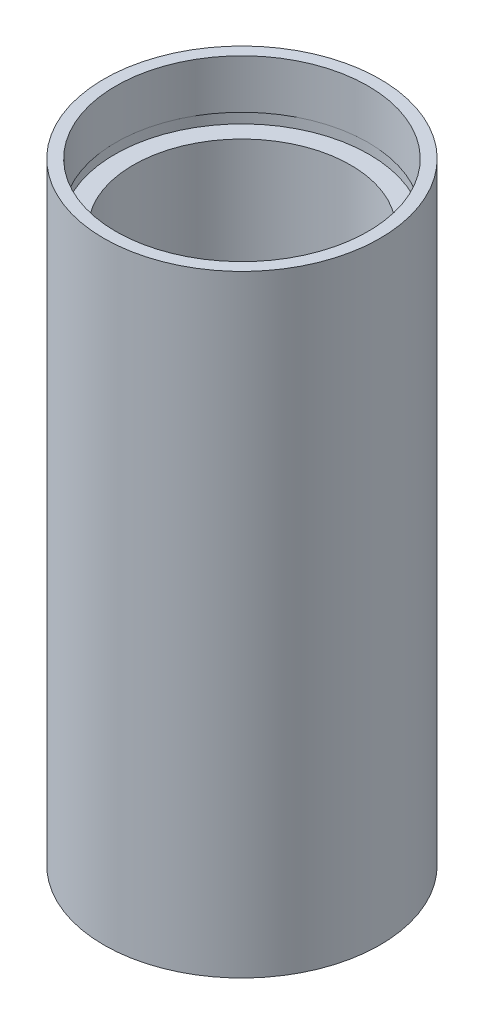
SolidWorks part; units mm, degrees
ref_plane "前视基准面" through (0, 0, 0) normal (0, 0, 1) x (1, 0, 0)
ref_plane "上视基准面" through (0, 0, 0) normal (0, 1, 0) x (1, 0, 0)
ref_plane "右视基准面" through (0, 0, 0) normal (1, 0, 0) x (0, 0, -1)
sketch "草图1" plane through (0, 0, 0) normal (0, 0, 1) x (1, 0, 0)
  line L0 (0, 161.3762) -> (0, 0) construction
  line L1 (141.7365, 0) -> (-131.7984, 0) construction
  line L2 (11.1, 0) -> (11.1, 4.5)
  line L3 (11.7, 4.5) -> (11.7, 5.5)
  line L4 (11.1, 4.5) -> (11.7, 4.5)
  line L5 (10, 5.5) -> (10, 50.8)
  line L6 (11.7, 5.5) -> (10, 5.5)
  line L7 (12.7, 0) -> (12.7, 56.3)
  line L8 (11.1, 0) -> (12.7, 0)
  line L9 (11.6, 56.3) -> (11.6, 51.8)
  line L10 (11.6, 56.3) -> (12.7, 56.3)
  line L11 (11.7, 51.8) -> (11.7, 50.8)
  line L12 (11.6, 51.8) -> (11.7, 51.8)
  line L13 (10, 50.8) -> (11.7, 50.8)
  point P15 (11.6, 54.05)
  dimension "D1" = 11.1
  dimension "D2" = 4.5
  dimension "D3" = 11.7
  dimension "D4" = 10
  dimension "D5" = 12.7
  dimension "D6" = 11.6
  dimension "D7" = 4.5
  dimension "D8" = 11.7
  dimension "D9" = 5.5
  dimension "D10" = 1
  dimension "D11" = 50.8
revolve "旋转1" add sketch "草图1" angle 360 about L0
cosmetic thread "装饰螺纹线1" parameters "D2"=23.2
cosmetic thread "装饰螺纹线2" parameters "D2"=21
cosmetic thread "装饰螺纹线3" parameters "D2"=23.21
